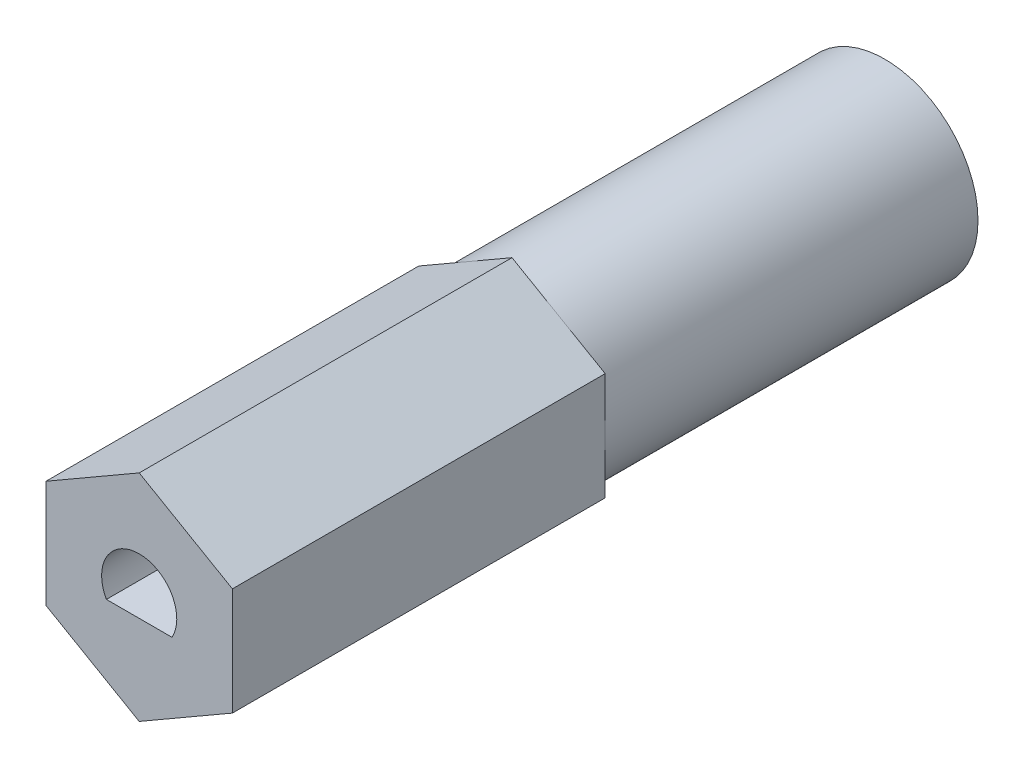
SolidWorks part; units mm, degrees
ref_plane "Front Plane" through (0, 0, 0) normal (0, 0, 1) x (1, 0, 0)
ref_plane "Top Plane" through (0, 0, 0) normal (0, 1, 0) x (1, 0, 0)
ref_plane "Right Plane" through (0, 0, 0) normal (1, 0, 0) x (0, 0, -1)
sketch "Sketch1" plane through (0, 0, 0) normal (0, 0, 1) x (1, 0, 0)
  line L1 (0, 3.6662) -> (-3.175, 1.8331)
  line L2 (-3.175, 1.8331) -> (-3.175, -1.8331)
  line L3 (-3.175, -1.8331) -> (0, -3.6662)
  line L4 (0, -3.6662) -> (3.175, -1.8331)
  line L5 (3.175, -1.8331) -> (3.175, 1.8331)
  line L6 (3.175, 1.8331) -> (0, 3.6662)
  circle A0 centre (0, 0) radius 3.175
  circle A1 centre (0, 0) radius 3.175 construction
  dimension "D1" = 6.35
extrude "Boss-Extrude1" add sketch "Sketch1" against normal blind 25.4 contours L1 L2 L3 L4 L5 L6
sketch "Sketch2" plane through (0, 0, 0) normal (0, 0, 1) x (1, 0, 0)
  line L0 (-1.1173, -0.6248) -> (1.1173, -0.6248)
  arc A0 (1.1173, -0.6248) -> (-1.1173, -0.6248) centre (0, 0) ccw
  dimension "D1" = 1.2802
  dimension "D2" = 1.905
extrude "Cut-Extrude1" cut sketch "Sketch2" against normal blind 5.08
ref_plane "Plane1" through (0, 0, -12.7) normal (0, 0, 1) x (1, 0, 0)
sketch "Sketch3" plane through (0, 0, -12.7) normal (0, 0, 1) x (1, 0, 0)
  circle A0 centre (0, 0) radius 3.175
  dimension "D1" = 6.35
extrude "Cut-Extrude2" cut sketch "Sketch3" against normal through all flip side to cut
